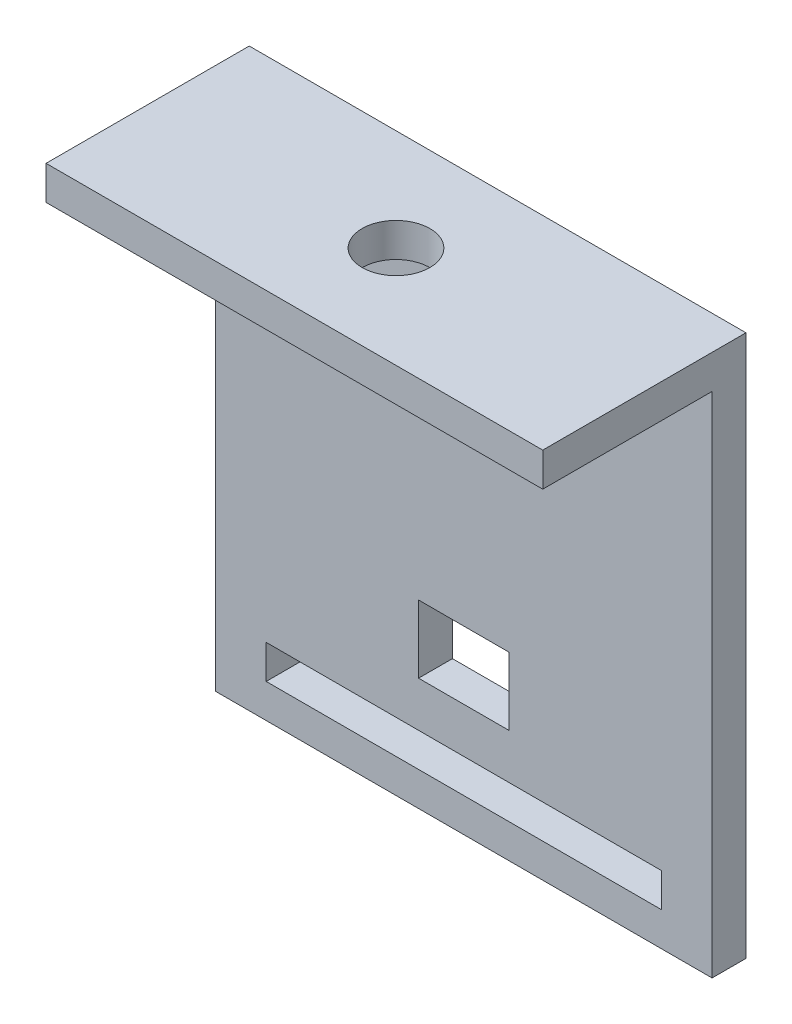
SolidWorks part; units mm, degrees
ref_plane "Piano frontale" through (0, 0, 0) normal (0, 0, 1) x (1, 0, 0)
ref_plane "Piano superiore" through (0, 0, 0) normal (0, 1, 0) x (1, 0, 0)
ref_plane "Piano destro" through (0, 0, 0) normal (1, 0, 0) x (0, 0, -1)
sketch "Schizzo8" plane through (0, 0, 0) normal (1, 0, 0) x (0, 0, -1)
  line L0 (0, 0) -> (0, 3)
  line L1 (0, 3) -> (18, 3)
  line L2 (18, 3) -> (18, -45)
  line L3 (18, -45) -> (15, -45)
  line L4 (15, -45) -> (15, 0)
  line L5 (15, 0) -> (0, 0)
  dimension "D1" = 3
  dimension "D2" = 18
  dimension "D3" = 45
  dimension "D4" = 3
extrude "Estrusione-Estrusione6" add sketch "Schizzo8" along normal blind 44
sketch "Schizzo9" plane through (0, 0, -15) normal (0, 0, 1) x (1, 0, 0)
  line L0 (44, -45) -> (0, -45) construction
  line L1 (4.5, -42) -> (39.5, -42)
  line L2 (4.5, -42) -> (4.5, -39)
  line L3 (4.5, -39) -> (39.5, -39)
  line L4 (39.5, -42) -> (39.5, -39)
  line L5 (0, 0) -> (0, -45) construction
  dimension "D1" = 3
  dimension "D2" = 35
  dimension "D3" = 3
  dimension "D4" = 4.5
extrude "Taglio-Estrusione2" cut sketch "Schizzo9" against normal blind 44
sketch "Schizzo10" plane through (0, 3, 0) normal (0, 1, 0) x (1, 0, 0)
  line L0 (0, 18) -> (44, 0) construction
  line L1 (44, 18) -> (44, 0) construction
  line L2 (44, 0) -> (44, 18) construction
  line L3 (44, 18) -> (0, 0) construction
  circle A0 centre (22, 9) radius 3
  dimension "D1" = 6
extrude "Taglio-Estrusione3" cut sketch "Schizzo10" against normal blind 10
sketch "Schizzo11" plane through (0, 0, -18) normal (0, 0, -1) x (-1, 0, 0)
  line L0 (-22, -39) -> (-22, -35) construction
  line L1 (-39.5, -39) -> (-4.5, -39) construction
  line L2 (-26, -35) -> (-18, -35)
  line L3 (-26, -35) -> (-26, -29)
  line L4 (-26, -29) -> (-18, -29)
  line L5 (-18, -29) -> (-18, -35)
  point P7 (-22, -35)
  dimension "D1" = 4
  dimension "D2" = 8
  dimension "D3" = 6
extrude "Taglio-Estrusione4" cut sketch "Schizzo11" against normal blind 10
